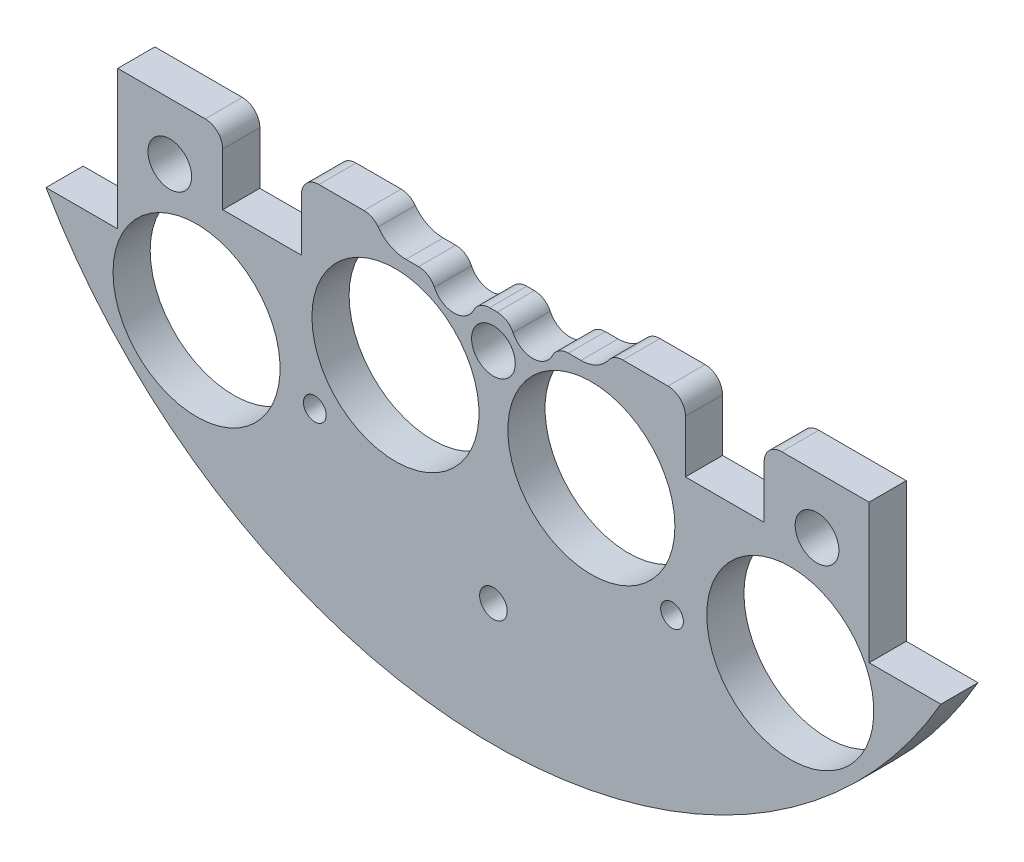
SolidWorks part; units mm, degrees
ref_plane "Front Plane" through (0, 0, 0) normal (0, 0, 1) x (1, 0, 0)
ref_plane "Top Plane" through (0, 0, 0) normal (0, 1, 0) x (1, 0, 0)
ref_plane "Right Plane" through (0, 0, 0) normal (1, 0, 0) x (0, 0, -1)
sketch "Sketch1" plane through (0, 0, 0) normal (0, 0, 1) x (1, 0, 0)
  line L0 (0, 0) -> (-82.1241, 0) construction
  line L1 (0, 0) -> (0, 95.6219) construction
  line L3 (-64.9644, 37.338) -> (-54.5504, 37.338)
  line L5 (-64.9644, -37.338) -> (-54.5504, -37.338)
  line L6 (-54.5504, 37.338) -> (-54.5504, -37.338)
  line L7 (64.9644, -37.338) -> (54.5504, -37.338)
  line L8 (64.9644, 37.338) -> (54.5504, 37.338)
  line L9 (54.5504, 37.338) -> (54.5504, -37.338)
  arc A0 (-64.9644, -37.338) -> (64.9644, -37.338) centre (0, 0) ccw
  circle A1 centre (-46.482, 11.049) radius 1.651
  circle A2 centre (-21.0833, 10.795) radius 1.651
  circle A3 centre (-21.0833, -10.795) radius 1.651
  circle A4 centre (-46.482, -11.049) radius 1.651
  circle A5 centre (46.482, -11.049) radius 1.651
  circle A6 centre (21.0833, -10.795) radius 1.651
  circle A7 centre (21.0833, 10.795) radius 1.651
  circle A8 centre (46.482, 11.049) radius 1.651
  arc A9 (64.9644, 37.338) -> (-64.9644, 37.338) centre (0, 0) ccw
  dimension "D2" = 3.302
  dimension "D3" = 3.302
  dimension "D4" = 25.4
  dimension "D5" = 10.795
  dimension "D10" = 46.482
  dimension "D6" = 74.676
  dimension "D7" = 10.414
  dimension "D8" = 74.93
  dimension "D9" = 74.93
  dimension "D11" = 37.338
extrude "Boss-Extrude2" add sketch "Sketch1" along normal blind 5.3975
sketch "Sketch2" plane through (0, 0, 5.3975) normal (0, 0, 1) x (1, 0, 0)
  line L0 (0, 68.58) -> (0, 55.88) construction
  line L1 (-9.525, 68.58) -> (9.525, 68.58)
  line L2 (-9.525, 68.58) -> (-9.525, 55.88)
  line L3 (-9.525, 55.88) -> (9.525, 55.88)
  line L4 (9.525, 68.58) -> (9.525, 55.88)
  line L5 (-9.525, 62.23) -> (9.525, 62.23) construction
  arc A0 (64.9644, 37.338) -> (-64.9644, 37.338) centre (0, 0) ccw construction
  circle A1 centre (-21.0833, 10.795) radius 1.651 construction
  circle A2 centre (21.0833, 10.795) radius 1.651 construction
  circle A3 centre (-6.731, 62.23) radius 1.143
  circle A4 centre (6.731, 62.23) radius 1.143
  dimension "D4" = 2.286
  dimension "D5" = 0
  dimension "D6" = 6.731
  dimension "D1" = 19.05
  dimension "D2" = 12.7
  dimension "D3" = 55.88
extrude "Cut-Extrude1" cut sketch "Sketch2" against normal through all contours A3 | A4
sketch "Sketch3" plane through (0, 0, 0) normal (0, 0, -1) x (-1, 0, 0)
  line L0 (0, 0) -> (0, -116.2908) construction
  line L1 (0, 0) -> (-153.8039, 0) construction
  line L2 (0, 0) -> (15.2681, -56.9814) construction
  circle A4 centre (-43.1052, -43.1052) radius 12.1285
  circle A6 centre (14.224, -34.29) radius 12.1285
  circle A7 centre (14.224, 34.29) radius 12.1285
  circle A8 centre (-43.1052, 43.1052) radius 12.1285
  circle A11 centre (43.1052, 43.1052) radius 12.1285
  circle A12 centre (-14.224, 34.29) radius 12.1285
  circle A13 centre (-14.224, -34.29) radius 12.1285
  circle A14 centre (43.1052, -43.1052) radius 12.1285
  point P36 (0, 0)
  point P53 (0, 0)
  point P55 (0, 0)
  dimension "D1" = 14.224
  dimension "D2" = 34.29
  dimension "D4" = 15
  dimension "D8" = 24.257
extrude "Cut-Extrude2" cut sketch "Sketch3" against normal through all
sketch "Sketch4" plane through (0, 0, 0) normal (0, 0, -1) x (-1, 0, 0)
  line L1 (-15.7702, 56.3138) -> (12.7925, 56.3138)
  line L2 (-15.7702, 56.3138) -> (-15.7702, 67.9913)
  line L3 (-15.7702, 67.9913) -> (12.7925, 67.9913)
  line L4 (12.7925, 56.3138) -> (12.7925, 67.9913)
extrude "Boss-Extrude3" add sketch "Sketch4" against normal up to surface (5.3975 mm away) up to face at (-55.2337, -43.1052, 5.3975)
sketch "Sketch5" plane through (0, 0, 0) normal (0, 0, -1) x (-1, 0, 0)
  line L1 (-85.044, -17.145) -> (131.6774, -17.145)
  line L2 (-85.044, -17.145) -> (-85.044, 113.4242)
  line L3 (-85.044, 113.4242) -> (131.6774, 113.4242)
  line L4 (131.6774, -17.145) -> (131.6774, 113.4242)
  circle A0 centre (-21.0833, -10.795) radius 1.651 construction
  dimension "D1" = 6.35
extrude "Cut-Extrude4" cut sketch "Sketch5" against normal through all contours L2 L3 L4 L1
sketch "Sketch6" plane through (0, 0, 0) normal (0, 0, -1) x (-1, 0, 0)
  line L0 (-33.02, -67.2621) -> (33.02, -67.2621)
  line L1 (0, 0) -> (0, -146.3858) construction
  arc A0 (-64.9644, -37.338) -> (64.9644, -37.338) centre (0, 0) ccw construction
  circle A1 centre (0, -86.3121) radius 38.1
  dimension "D2" = 76.2
  dimension "D1" = 66.04
  dimension "D3" = 19.05
sketch "Sketch7" plane through (0, 0, 0) normal (0, 0, -1) x (-1, 0, 0)
  line L0 (0, 0) -> (0, -146.3858) construction
  line L3 (-54.5504, -17.145) -> (54.5504, -17.145) construction
  circle A0 centre (0, -57.145) radius 2
  dimension "D1" = 4
  dimension "D2" = 40
extrude "Cut-Extrude5" cut sketch "Sketch7" against normal blind 23.368 contours A0
extrude "Cut-Extrude6" cut sketch "Sketch8" against normal through all both and the other way through all
sketch "Sketch8" plane through (-31.3134, 132.614, 19.05) normal (0, 0, 1) x (0, 1, 0)
  line L0 (-132.614, -31.3134) -> (-132.614, 57.8454) construction
  line L1 (-132.614, -31.3134) -> (-222.516, -31.3134) construction
  circle A0 centre (-158.014, 14.4066) radius 3.175
  circle A1 centre (-173.254, -31.3134) radius 3.175
  circle A3 centre (-158.014, -77.0334) radius 3.175
  circle A4 centre (-107.214, -77.0334) radius 3.175
  circle A5 centre (-91.974, -31.3134) radius 3.175
  circle A6 centre (-107.214, 14.4066) radius 3.175
extrude "Cut-Extrude7" cut sketch "Sketch9" against normal blind 29.21
sketch "Sketch9" plane through (-31.3134, 132.559, 15.875) normal (0, 0, 1) x (0, 1, 0)
  line L0 (-132.559, -31.3134) -> (6.1626, -31.3134) construction
  line L2 (-132.559, -31.3134) -> (-132.559, -122.6589) construction
  circle A0 centre (-190.979, 2.9766) radius 1.651
  circle A2 centre (-154.784, -31.3134) radius 1.651
  circle A3 centre (-190.979, -65.6034) radius 1.651
  circle A4 centre (-110.334, -31.3134) radius 1.651
  circle A5 centre (-74.139, -65.6034) radius 1.651
  circle A6 centre (-74.139, 2.9766) radius 1.651
sketch "Sketch11" plane through (0, 0, 0) normal (0, 0, -1) x (-1, 0, 0)
  line L0 (-54.5504, -17.145) -> (54.5504, -17.145) construction
  line L1 (-39.3104, -17.145) -> (-27.8804, -17.145)
  line L2 (-39.3104, -17.145) -> (-39.3104, -27.305)
  line L3 (-39.3104, -27.305) -> (-27.8804, -27.305)
  line L4 (-27.8804, -17.145) -> (-27.8804, -27.305)
  line L5 (-54.5504, -37.338) -> (-54.5504, -17.145) construction
  line L6 (27.8804, -17.145) -> (39.3104, -17.145)
  line L7 (27.8804, -17.145) -> (27.8804, -27.305)
  line L8 (27.8804, -27.305) -> (39.3104, -27.305)
  line L9 (39.3104, -17.145) -> (39.3104, -27.305)
  line L10 (0, -5.5068) -> (0, -79.5506) construction
  dimension "D1" = 10.16
  dimension "D2" = 11.43
  dimension "D3" = 15.24
extrude "Cut-Extrude9" cut sketch "Sketch11" against normal through all
extrude "Cut-Extrude65" cut sketch "Sketch67" against normal blind 97.79
sketch "Sketch67" plane through (30.092, 4.0835, -19.2405) normal (0, 0, -1) x (-1, 0, 0)
  line L0 (30.092, -29.4835) -> (30.092, 6.2385) construction
  circle A0 centre (4.1544, -49.7288) radius 1.651
  circle A4 centre (56.0296, -49.7288) radius 1.651
  circle A5 centre (4.1544, 41.3825) radius 1.651
  circle A9 centre (56.0296, 41.3825) radius 1.651
extrude "Cut-Extrude119" cut sketch "Sketch121" against normal blind 48.768 and the other way blind 103.378
sketch "Sketch121" plane through (30.092, 4.0835, 16.891) normal (0, 0, -1) x (-1, 0, 0)
  line L0 (30.092, -4.0835) -> (148.6336, -4.0835) construction
  line L1 (30.092, -4.0835) -> (30.092, 90.452) construction
  circle A0 centre (-16.898, 21.3165) radius 3.175
  circle A1 centre (77.082, 21.3165) radius 3.175
  circle A2 centre (30.092, 21.3165) radius 3.175
  circle A4 centre (77.082, -29.4835) radius 3.175
  circle A5 centre (30.092, -29.4835) radius 3.175
  circle A6 centre (-16.898, -29.4835) radius 3.175
sketch "Sketch14" plane through (0, 0, 5.3975) normal (0, 0, 1) x (1, 0, 0)
  line L0 (0, 0) -> (0, 24.494) construction
  line L1 (12.7, -20.24) -> (8.889, -20.24)
  line L2 (7.7, -15.24) -> (-7.7, -15.24)
  line L3 (-8.889, -20.24) -> (-12.7, -20.24)
  line L4 (2.541, -20.24) -> (-2.541, -20.24)
  arc A0 (12.7, -20.24) -> (7.7, -15.24) centre (12.7, -15.24) ccw
  arc A1 (-12.7, -20.24) -> (-7.7, -15.24) centre (-12.7, -15.24) cw
  arc A2 (2.541, -20.24) -> (8.889, -20.24) centre (5.715, -20.32) ccw
  arc A3 (-8.889, -20.24) -> (-2.541, -20.24) centre (-5.715, -20.32) ccw
  dimension "D1" = 10
  dimension "D4" = 6.35
  dimension "D5" = 6.35
  dimension "D2" = 12.7
  dimension "D3" = 15.24
  dimension "D6" = 11.43
  dimension "D7" = 5.715
  dimension "D8" = 20.32
extrude "Cut-Extrude12" cut sketch "Sketch14" against normal blind 10
fillet "Fillet1" radius 2.54 10 edges at (-39.3104, -17.145, 2.6987) (-27.8804, -17.145, 2.6987) (-17.3229, -17.145, 2.6987) (-8.889, -20.24, 2.6987) (-2.541, -20.24, 2.6987) (2.541, -20.24, 2.6987) (8.889, -20.24, 2.6987) (17.3229, -17.145, 2.6987) (27.8804, -17.145, 2.6987) (39.3104, -17.145, 2.6987)
